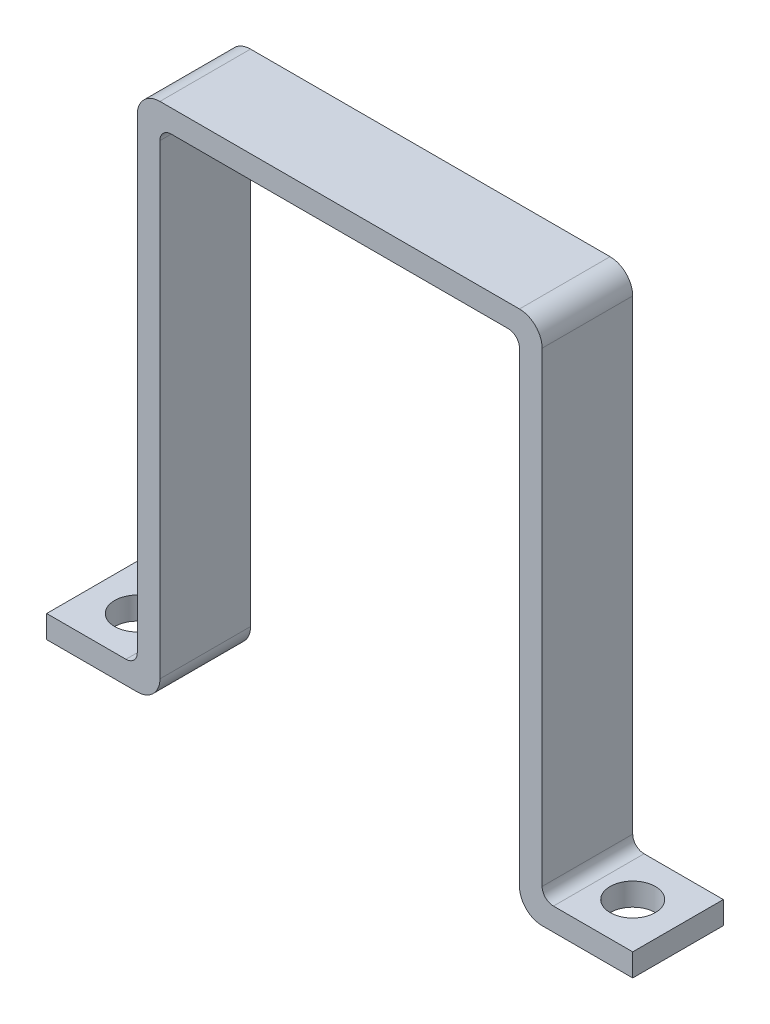
SolidWorks part; units mm, degrees
material "6061-T6 (SS)"
ref_plane "Front Plane" through (0, 0, 0) normal (0, 0, 1) x (1, 0, 0)
ref_plane "Top Plane" through (0, 0, 0) normal (0, 1, 0) x (1, 0, 0)
ref_plane "Right Plane" through (0, 0, 0) normal (1, 0, 0) x (0, 0, -1)
sketch "Sketch1" plane through (0, 0, 0) normal (0, 1, 0) x (1, 0, 0)
  line L0 (172.0579, 97.5158) -> (178.6079, 97.5158) construction
  line L1 (178.6079, 97.5158) -> (185.1579, 97.5158) construction
  line L2 (168.8829, 138.7908) -> (187.8487, 119.8251)
  line L3 (210.1579, 122.5158) -> (210.1579, 129.0658) construction
  line L4 (210.1579, 129.0658) -> (210.1579, 135.6158) construction
  line L5 (210.1579, 97.5158) -> (168.8829, 138.7908)
  line L6 (210.1579, 97.5158) -> (187.8487, 119.8251)
  line L7 (210.1579, 97.5158) -> (185.6036, 72.9616)
  line L8 (210.1579, 97.5158) -> (234.7122, 122.0701)
  line L9 (210.1579, 97.5158) -> (185.6036, 122.0701)
  line L10 (0, 0) -> (-34.725, 0)
  line L11 (-34.725, 0) -> (-69.45, 0)
  line L13 (-75.8, -6.35) -> (-63.1, -6.35)
  line L14 (-75.8, -6.35) -> (-75.8, 6.35)
  line L15 (-75.8, 6.35) -> (-63.1, 6.35)
  line L16 (-63.1, -6.35) -> (-63.1, 6.35)
  line L17 (-75.8, -6.35) -> (-63.1, 6.35) construction
  line L18 (-75.8, 6.35) -> (-63.1, -6.35) construction
  line L19 (-6.35, -6.35) -> (6.35, -6.35)
  line L20 (-6.35, -6.35) -> (-6.35, 6.35)
  line L21 (-6.35, 6.35) -> (6.35, 6.35)
  line L22 (6.35, -6.35) -> (6.35, 6.35)
  line L23 (-6.35, -6.35) -> (6.35, 6.35) construction
  line L24 (-6.35, 6.35) -> (6.35, -6.35) construction
  line L25 (-63.1, 6.35) -> (-59.925, 6.35)
  line L26 (-63.1, 6.35) -> (-63.1, -6.35)
  line L27 (-63.1, -6.35) -> (-59.925, -6.35)
  line L28 (-59.925, 6.35) -> (-59.925, -6.35)
  line L29 (-6.35, 6.35) -> (-9.525, 6.35)
  line L30 (-6.35, 6.35) -> (-6.35, -6.35)
  line L31 (-6.35, -6.35) -> (-9.525, -6.35)
  line L32 (-9.525, 6.35) -> (-9.525, -6.35)
  circle A0 centre (0, 0) radius 3.175
  circle A1 centre (210.1579, 97.5158) radius 26.25
  circle A2 centre (210.1579, 97.5158) radius 25 construction
  circle A3 centre (210.1579, 97.5158) radius 38.1
  circle A4 centre (210.1579, 97.5158) radius 31.55
  circle A5 centre (210.1579, 97.5158) radius 34.725
  circle A6 centre (185.6036, 122.0701) radius 3.175
  circle A7 centre (234.7122, 122.0701) radius 3.175
  circle A8 centre (185.6036, 72.9616) radius 3.175
  circle A9 centre (-69.45, 0) radius 3.175
  circle A10 centre (-34.725, 0) radius 25
  point P24 (210.1579, 97.5158)
  dimension "D1" = 76.2
  dimension "D2" = 6.35
  dimension "D3" = 6.35
  dimension "D4" = 6.35
  dimension "D7" = 6.35
  dimension "D9" = 6.35
  dimension "D12" = 12.7
  dimension "D14" = 50
  dimension "D5" = 34.725
  dimension "D6" = 34.725
  dimension "D8" = 34.725
  dimension "D10" = 12.7
  dimension "D11" = 12.7
  dimension "D13" = 12.7
  dimension "D15" = 3.175
  dimension "D16" = 3.175
extrude "Boss-Extrude1" add sketch "Sketch1" along normal blind 3.175
sketch "Sketch2" plane through (0, 3.175, 0) normal (0, 1, 0) x (1, 0, 0)
  line L0 (6.35, 6.35) -> (-9.525, 6.35) construction
  line L1 (-9.525, 6.35) -> (-9.525, -6.35) construction
  line L2 (-9.525, -6.35) -> (6.35, -6.35) construction
  line L3 (6.35, -6.35) -> (6.35, 6.35) construction
  line L4 (-75.8, -6.35) -> (-59.925, -6.35) construction
  line L5 (-59.925, -6.35) -> (-59.925, 6.35) construction
  line L6 (-59.925, 6.35) -> (-75.8, 6.35) construction
  line L7 (-75.8, 6.35) -> (-75.8, -6.35) construction
  line L8 (6.35, 6.35) -> (-9.525, 6.35)
  line L9 (-9.525, 6.35) -> (-9.525, -6.35)
  line L10 (-9.525, -6.35) -> (6.35, -6.35)
  line L11 (6.35, -6.35) -> (6.35, 6.35)
  line L12 (-75.8, -6.35) -> (-59.925, -6.35)
  line L13 (-59.925, -6.35) -> (-59.925, 6.35)
  line L14 (-59.925, 6.35) -> (-75.8, 6.35)
  line L15 (-75.8, 6.35) -> (-75.8, -6.35)
  line L17 (-59.925, 6.35) -> (-63.1, 6.35)
  line L18 (-59.925, 6.35) -> (-59.925, -6.35)
  line L19 (-59.925, -6.35) -> (-63.1, -6.35)
  line L20 (-63.1, 6.35) -> (-63.1, -6.35)
  line L21 (-9.525, 6.35) -> (-6.35, 6.35)
  line L22 (-9.525, 6.35) -> (-9.525, -6.35)
  line L23 (-9.525, -6.35) -> (-6.35, -6.35)
  line L24 (-6.35, 6.35) -> (-6.35, -6.35)
  line M7 (-59.925, -6.35) -> (-59.925, 6.35)
  line M8 (-59.925, 6.35) -> (-75.8, 6.35)
  dimension "D1" = 3.175
  dimension "D2" = 3.175
extrude "Boss-Extrude2" add sketch "Sketch2" along normal blind 70.104 contours L20 L12 M8 M7 | L24 L8 L9 L10
sketch "Sketch3" plane through (0, 73.279, 0) normal (0, 1, 0) x (1, 0, 0)
  line L1 (-63.1, 6.35) -> (-6.35, 6.35)
  line L2 (-63.1, 6.35) -> (-63.1, -6.35)
  line L3 (-63.1, -6.35) -> (-6.35, -6.35)
  line L4 (-59.925, 6.35) -> (-63.1, 6.35)
  line L5 (-63.1, 6.35) -> (-63.1, -6.35)
  line L6 (-63.1, -6.35) -> (-59.925, -6.35)
  line L7 (-59.925, -6.35) -> (-59.925, 6.35)
  line L8 (-59.925, 6.35) -> (-63.1, 6.35)
  line L9 (-63.1, 6.35) -> (-63.1, -6.35)
  line L10 (-63.1, -6.35) -> (-59.925, -6.35)
  line L11 (-59.925, -6.35) -> (-59.925, 6.35)
  line L12 (-6.35, 6.35) -> (-6.35, -6.35)
  line M5 (-59.925, 6.35) -> (-63.1, 6.35)
  line M6 (-63.1, 6.35) -> (-63.1, -6.35)
  line M7 (-63.1, -6.35) -> (-59.925, -6.35)
  line M8 (-59.925, -6.35) -> (-59.925, 6.35)
  dimension "D1" = 0
extrude "Boss-Extrude3" add sketch "Sketch3" against normal blind 3.175 contours M8 M5 M6 M7 | L12 L1 L3 M8
fillet "Fillet5" radius 3.175 4 edges at (-59.925, 0, 0) (-9.525, 0, 0) (-63.1, 73.279, 0) (-6.35, 73.279, 0)
fillet "Fillet6" radius 1.5875 4 edges at (-63.1, 3.175, 0) (-6.35, 3.175, 0) (-59.925, 70.104, 0) (-9.525, 70.104, 0)
